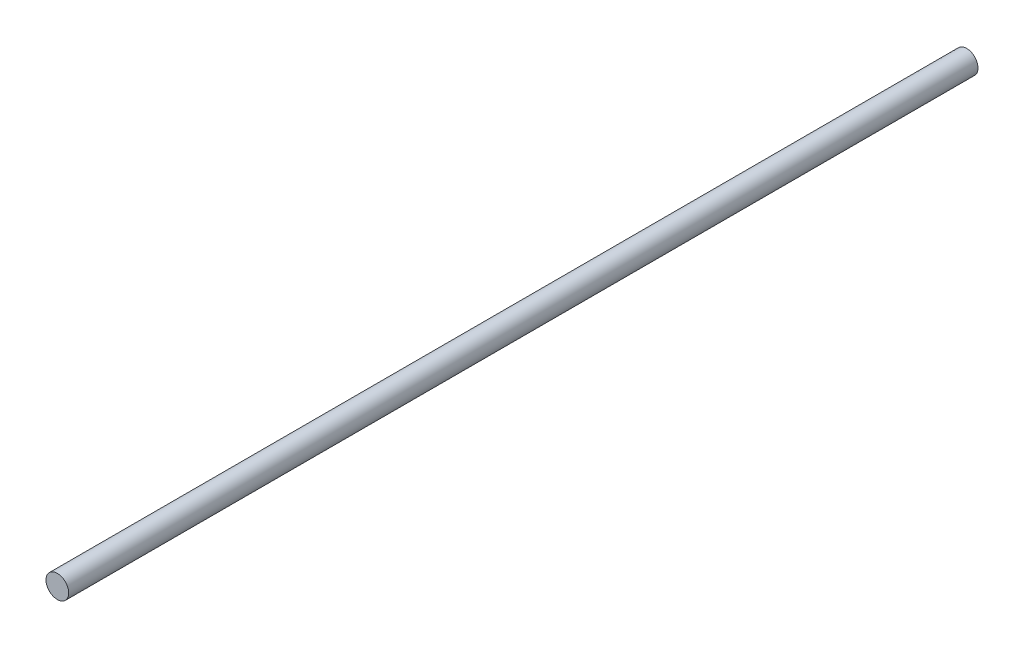
SolidWorks part; units mm, degrees
ref_plane "Alzado" through (0, 0, 0) normal (0, 0, 1) x (1, 0, 0)
ref_plane "Planta" through (0, 0, 0) normal (0, 1, 0) x (1, 0, 0)
ref_plane "Vista lateral" through (0, 0, 0) normal (1, 0, 0) x (0, 0, -1)
sketch "Croquis1" plane through (0, 0, 0) normal (0, 0, 1) x (1, 0, 0)
  circle A0 centre (0, 0) radius 4
  dimension "D1" = 8
extrude "Saliente-Extruir1" add sketch "Croquis1" along normal blind 320
